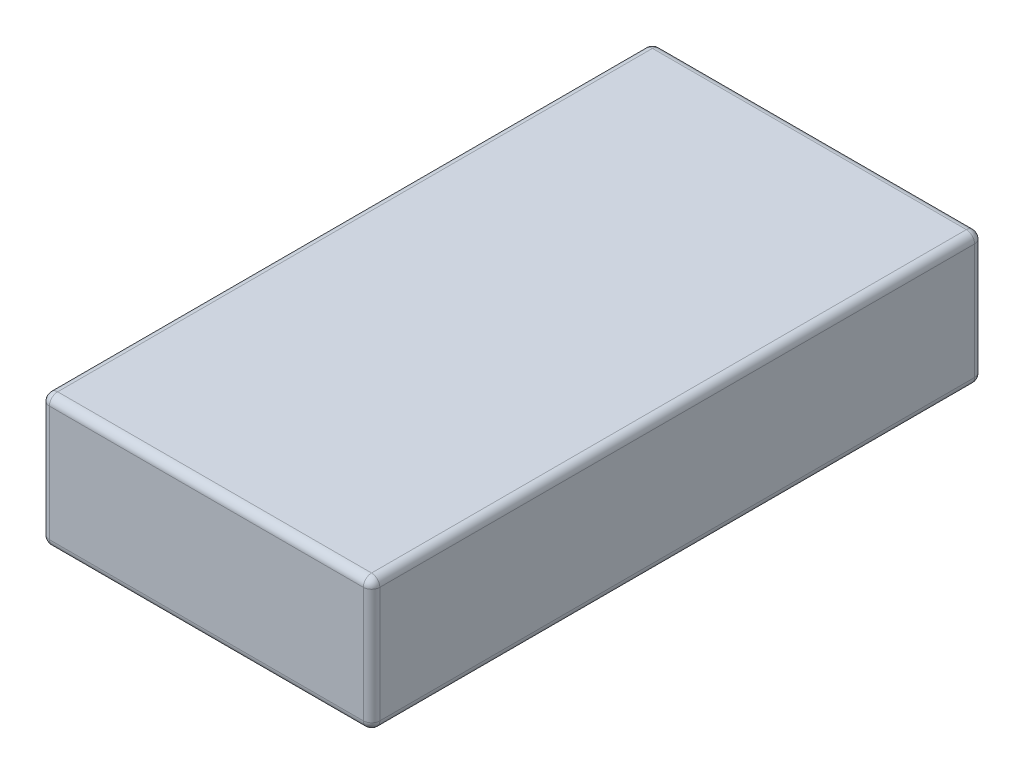
SolidWorks part; units mm, degrees
ref_plane "Front Plane" through (0, 0, 0) normal (0, 0, 1) x (1, 0, 0)
ref_plane "Top Plane" through (0, 0, 0) normal (0, 1, 0) x (1, 0, 0)
ref_plane "Right Plane" through (0, 0, 0) normal (1, 0, 0) x (0, 0, -1)
sketch "Sketch1" plane through (0, 0, 0) normal (0, 1, 0) x (1, 0, 0)
  line L1 (-10, -18.5) -> (10, -18.5)
  line L2 (-10, -18.5) -> (-10, 18.5)
  line L3 (-10, 18.5) -> (10, 18.5)
  line L4 (10, -18.5) -> (10, 18.5)
  line L5 (-10, -18.5) -> (10, 18.5) construction
  line L6 (-10, 18.5) -> (10, -18.5) construction
  point P0 (0, 0)
  dimension "D1" = 20
  dimension "D2" = 37
extrude "Boss-Extrude1" add sketch "Sketch1" along normal blind 8
fillet "Fillet1" radius 0.5 12 edges at (-10, 4, -18.5) (-10, 4, 18.5) (10, 4, 18.5) (10, 4, -18.5) (0, 0, -18.5) (-10, 0, 0) (0, 0, 18.5) (10, 0, 0) (0, 8, 18.5) (-10, 8, 0) (0, 8, -18.5) (10, 8, 0)
